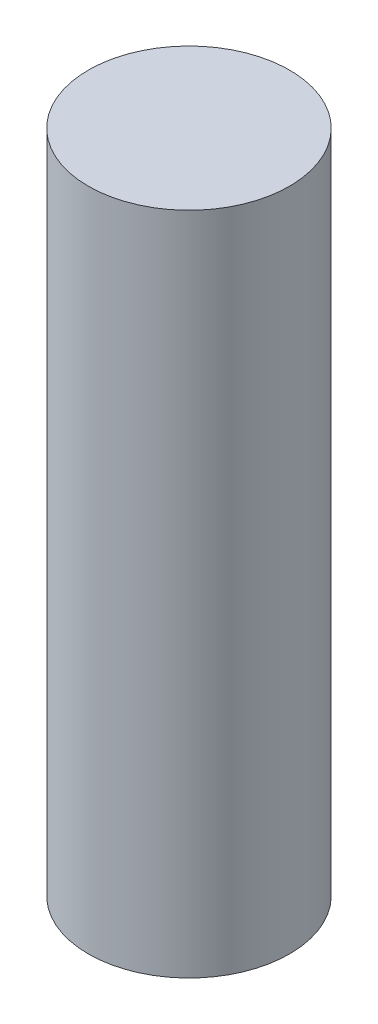
SolidWorks part; units mm, degrees
material "6061-T6 (SS)"
ref_plane "Front Plane" through (0, 0, 0) normal (0, 0, 1) x (1, 0, 0)
ref_plane "Top Plane" through (0, 0, 0) normal (0, 1, 0) x (1, 0, 0)
ref_plane "Right Plane" through (0, 0, 0) normal (1, 0, 0) x (0, 0, -1)
sketch "Sketch1" plane through (0, 0, 0) normal (0, 1, 0) x (1, 0, 0)
  circle A0 centre (0, 0) radius 18.2562
  dimension "D1" = 36.5125
extrude "Boss-Extrude1" add sketch "Sketch1" along normal blind 120.65
chamfer "Chamfer1" [suppressed] distance 5.5562 distance2 25.4
